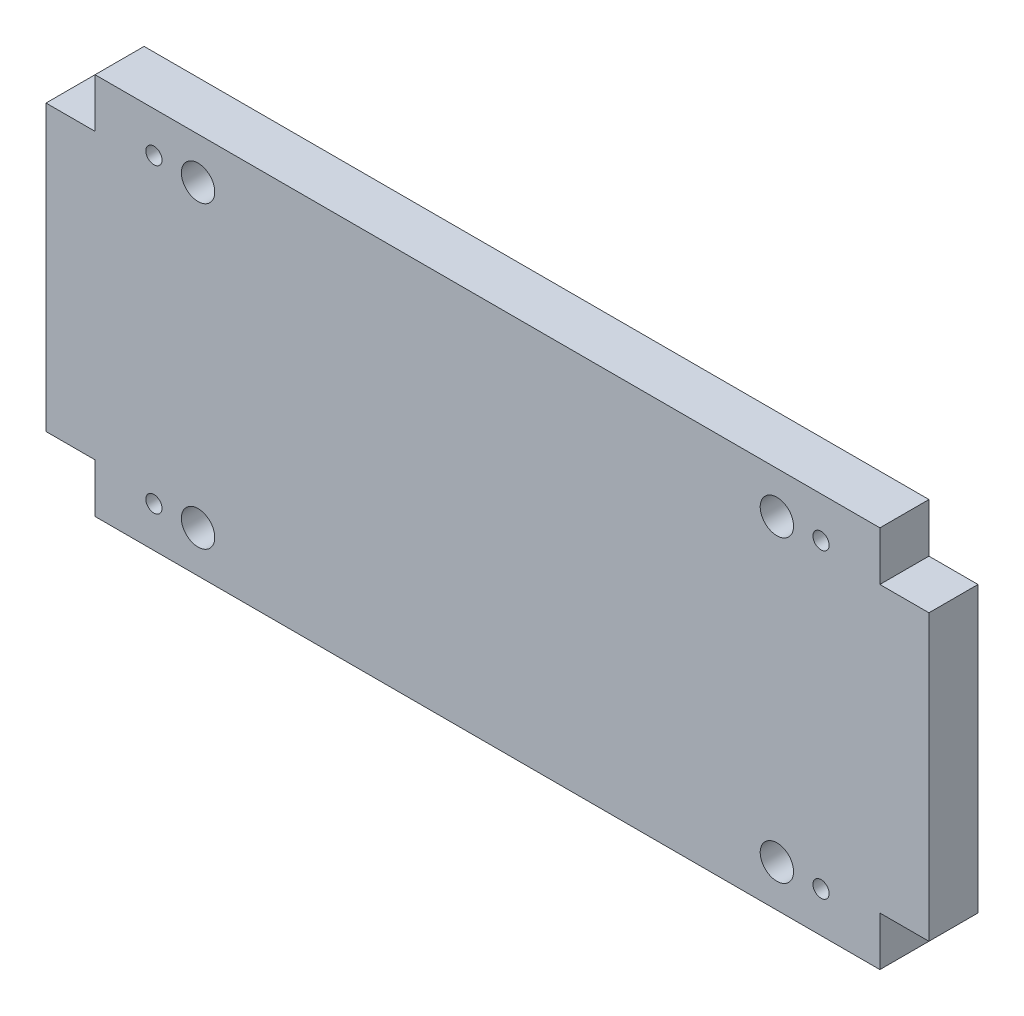
SolidWorks part; units mm, degrees
ref_plane "Front Plane" through (0, 0, 0) normal (0, 0, 1) x (1, 0, 0)
ref_plane "Top Plane" through (0, 0, 0) normal (0, 1, 0) x (1, 0, 0)
ref_plane "Right Plane" through (0, 0, 0) normal (1, 0, 0) x (0, 0, -1)
sketch "Sketch1" plane through (0, 0, 0) normal (0, 0, 1) x (1, 0, 0)
  line L0 (0, 39) -> (0, -39) construction
  line L1 (-80, 39) -> (80, 39)
  line L2 (-80, 39) -> (-80, 29)
  line L3 (-80, -39) -> (80, -39)
  line L4 (80, 39) -> (80, 29)
  line L5 (-80, 39) -> (80, -39) construction
  line L6 (-80, -39) -> (80, 39) construction
  line L7 (-80, 29) -> (-90, 29)
  line L8 (-90, 29) -> (-90, -29)
  line L9 (-90, -29) -> (-80, -29)
  line L10 (-80, -29) -> (-80, -39)
  line L11 (90, -29) -> (80, -29)
  line L12 (90, 29) -> (90, -29)
  line L13 (80, 29) -> (90, 29)
  line L14 (80, -29) -> (80, -39)
  line L15 (-90, 0) -> (90, 0) construction
  point P0 (0, 0)
  dimension "D4" = 10
  dimension "D1" = 160
  dimension "D2" = 78
  dimension "D3" = 10
extrude "Boss-Extrude1" add sketch "Sketch1" along normal blind 10
hole_wizard "M4 Tapped Hole1" positions "Sketch2" profile "Sketch3" tap size "M4" standard "ISO" end condition through all
sketch "Sketch2" plane through (0, 0, 10) normal (0, 0, 1) x (1, 0, 0)
  line L0 (-90, 0) -> (90, 0) construction
  line L1 (-90, 29) -> (-90, -29) construction
  line L2 (90, -29) -> (90, 29) construction
  line L4 (0, 39) -> (0, -38.3907) construction
  line L5 (80, 39) -> (-80, 39) construction
  line L7 (-80, 39) -> (-80, 29) construction
  point P0 (-68, 30.75)
  point P18 (-68, -30.75)
  point P20 (68, -30.75)
  point P21 (68, 30.75)
  dimension "D1" = 8.25
  dimension "D2" = 12
sketch "Sketch3" plane through (-68, 30.75, 10) normal (1, 0, 0) x (0, -1, 0)
  line L0 (0, 0) -> (0, 10)
  line L1 (0, 10) -> (1.65, 10)
  line L2 (1.65, 10) -> (1.65, 0)
  line L5 (1.65, 0) -> (0, 0)
  line L11 (0, -6.35) -> (0, 107.95) construction
  dimension "Thru Tap Drill Dia." = 3.3
  dimension "Thru Tap Drill Depth" = 10
cosmetic thread "Hole Thread1" parameters "D2"=4
cosmetic thread "Hole Thread2" parameters "D2"=4
cosmetic thread "Hole Thread3" parameters "D2"=4
cosmetic thread "Hole Thread4" parameters "D2"=4
hole_wizard "M8 Tapped Hole1" positions "Sketch4" profile "Sketch5" tap size "M8" standard "ISO" end condition through all
sketch "Sketch4" plane through (0, 0, 10) normal (0, 0, 1) x (1, 0, 0)
  line L0 (0, 39) -> (0, -39) construction
  line L1 (80, 39) -> (-80, 39) construction
  line L2 (-80, -39) -> (80, -39) construction
  line L4 (-90, 0) -> (90, 0) construction
  line L5 (-90, 29) -> (-90, -29) construction
  line L6 (90, -29) -> (90, 29) construction
  point P0 (-59, 30.5)
  point P18 (-59, -30.5)
  point P19 (59, -30.5)
  point P20 (59, 30.5)
  dimension "D1" = 59
  dimension "D2" = 8.5
sketch "Sketch5" plane through (-59, 30.5, 10) normal (1, 0, 0) x (0, -1, 0)
  line L0 (0, 0) -> (0, 10)
  line L1 (0, 10) -> (3.4, 10)
  line L2 (3.4, 10) -> (3.4, 0)
  line L5 (3.4, 0) -> (0, 0)
  line L11 (0, -6.35) -> (0, 107.95) construction
  dimension "Thru Tap Drill Dia." = 6.8
  dimension "Thru Tap Drill Depth" = 10
cosmetic thread "Hole Thread5" parameters "D2"=8
cosmetic thread "Hole Thread6" parameters "D2"=8
cosmetic thread "Hole Thread7" parameters "D2"=8
cosmetic thread "Hole Thread8" parameters "D2"=8
